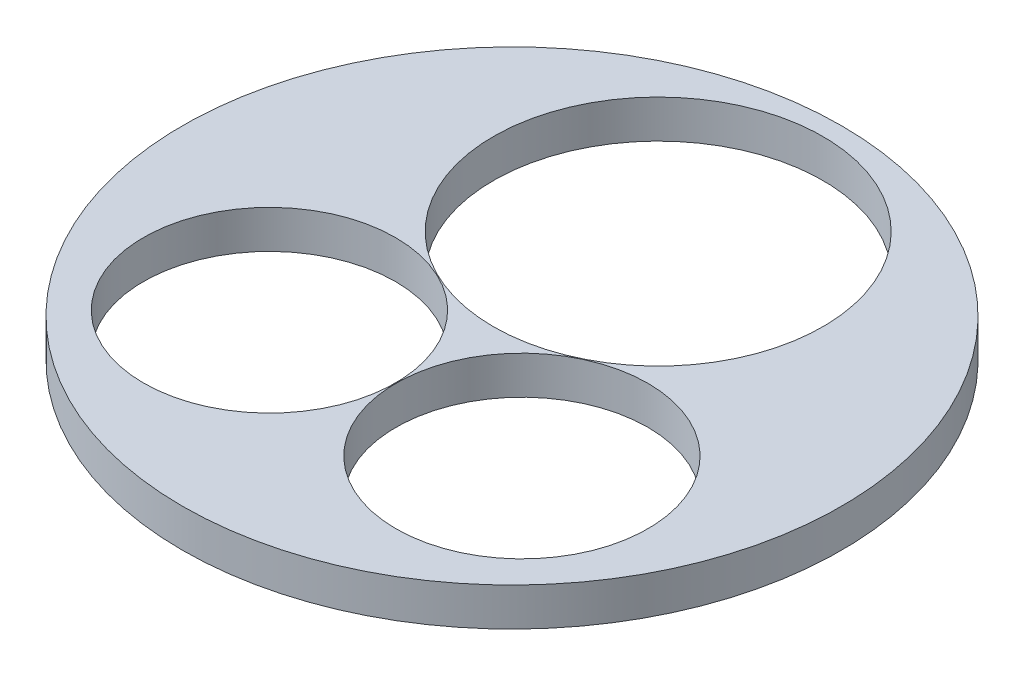
SolidWorks part; units mm, degrees
material "7075-T6 (SN)"
ref_plane "Front Plane" through (0, 0, 0) normal (0, 0, 1) x (1, 0, 0)
ref_plane "Top Plane" through (0, 0, 0) normal (0, 1, 0) x (1, 0, 0)
ref_plane "Right Plane" through (0, 0, 0) normal (1, 0, 0) x (0, 0, -1)
sketch "Sketch1" plane through (0, 0, 0) normal (0, 1, 0) x (1, 0, 0)
  line L0 (-330.835, -304.8) -> (0, 0) construction
  line L1 (-330.835, -304.8) -> (330.835, -304.8) construction
  line L2 (330.835, -304.8) -> (0, 383.0439) construction
  line L3 (0, 383.0439) -> (-330.835, -304.8) construction
  line L4 (0, 0) -> (330.835, -304.8) construction
  circle A2 centre (330.835, -304.8) radius 330.2
  circle A5 centre (0, 0) radius 863.6
  circle A6 centre (0, 383.0439) radius 431.8
  circle A8 centre (-330.835, -304.8) radius 330.2
  dimension "D1" = 1727.2
  dimension "D2" = 304.8
  dimension "D3" = 660.4
  dimension "D4" = 660.4
  dimension "D5" = 863.6
  dimension "D7" = 661.67
  dimension "D8" = 763.27
  dimension "D9" = 763.27
extrude "Boss-Extrude1" add sketch "Sketch1" along normal blind 100
